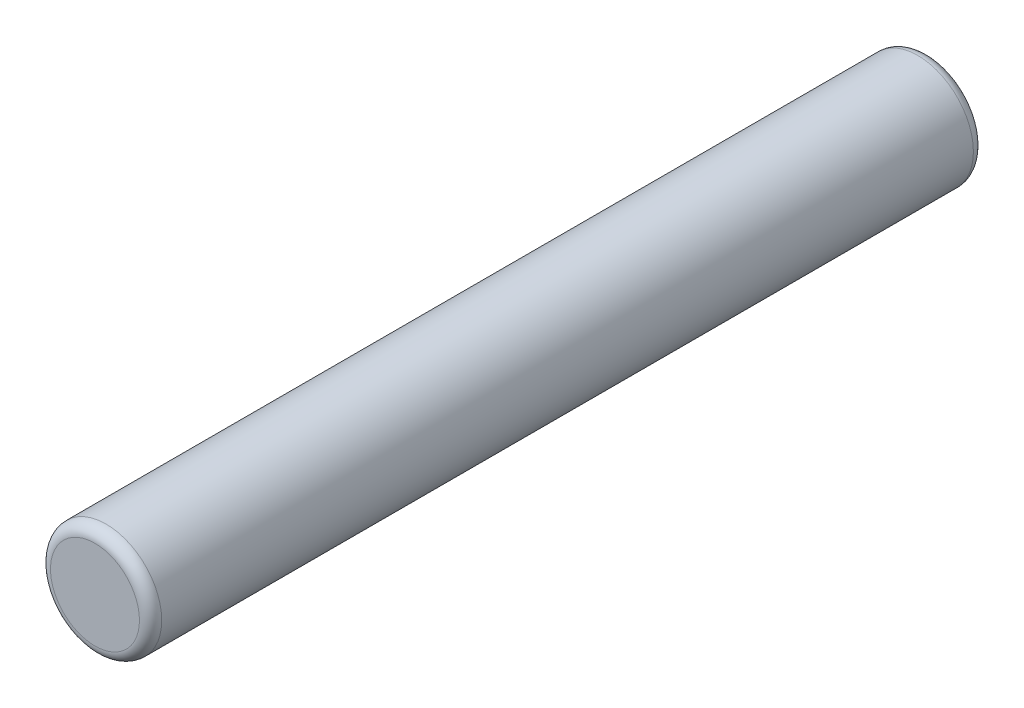
SolidWorks part; units mm, degrees
ref_plane "Front Plane" through (0, 0, 0) normal (0, 0, 1) x (1, 0, 0)
ref_plane "Top Plane" through (0, 0, 0) normal (0, 1, 0) x (1, 0, 0)
ref_plane "Right Plane" through (0, 0, 0) normal (1, 0, 0) x (0, 0, -1)
sketch "Sketch2" plane through (0, 0, 0) normal (0, 0, 1) x (1, 0, 0)
  circle A0 centre (-17.8581, 10.9478) radius 1
extrude "Boss-Extrude1" add sketch "Sketch2" along normal blind 15
fillet "Fillet1" radius 0.2 2 edges at (-16.8581, 10.9478, 0) (-16.8581, 10.9478, 15)
